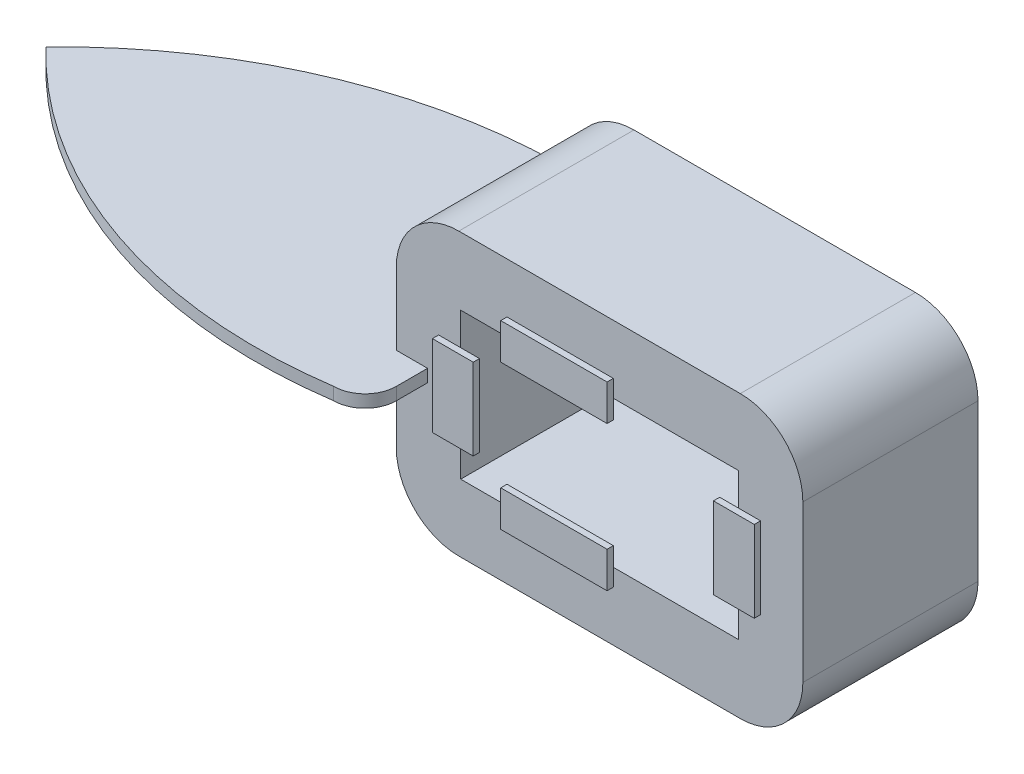
SolidWorks part; units mm, degrees
ref_plane "前基準面" through (0, 0, 0) normal (0, 0, 1) x (1, 0, 0)
ref_plane "上基準面" through (0, 0, 0) normal (0, 1, 0) x (1, 0, 0)
ref_plane "右基準面" through (0, 0, 0) normal (1, 0, 0) x (0, 0, -1)
sketch "草圖1" plane through (0, 0, 0) normal (0, 0, 1) x (1, 0, 0)
  line L0 (-9.02, 0) -> (7.9922, 0) construction
  line L2 (-59.9347, 22.5) -> (5.0653, 22.5)
  line L3 (-59.9347, 22.5) -> (-59.9347, -22.5)
  line L4 (-59.9347, -22.5) -> (5.0653, -22.5)
  line L5 (5.0653, 22.5) -> (5.0653, -22.5)
  dimension "D1" = 45
  dimension "D2" = 22.5
  dimension "D3" = 65
extrude "填料-伸長1" add sketch "草圖1" along normal blind 28
sketch "草圖2" plane through (0, 0, 0) normal (0, 0, 1) x (1, 0, 0)
  line L0 (-59.9347, 0) -> (5.361, 0) construction
  line L1 (-59.9347, 22.5) -> (-59.9347, -22.5) construction
  line L2 (-27.4347, 22.5) -> (-27.4347, -22.5) construction
  line L3 (5.0653, 22.5) -> (-59.9347, 22.5) construction
  line L4 (-59.9347, -22.5) -> (5.0653, -22.5) construction
  line L6 (-49.6347, 11.7) -> (-5.2347, 11.7)
  line L7 (-49.6347, 11.7) -> (-49.6347, -11.7)
  line L8 (-49.6347, -11.7) -> (-5.2347, -11.7)
  line L9 (-5.2347, 11.7) -> (-5.2347, -11.7)
  dimension "D1" = 44.4
  dimension "D2" = 23.4
  dimension "D3" = 10.3
  dimension "D4" = 10.8
extrude "除料-伸長1" cut sketch "草圖2" along normal blind 39
ref_plane "平面1" through (0, 0, 28) normal (0, 0, 1) x (1, 0, 0)
sketch "草圖3" plane through (0, 0, 28) normal (0, 0, 1) x (1, 0, 0)
  line L0 (-59.9347, 22.5) -> (-59.9347, -22.5) construction
  line L2 (-59.9347, 12) -> (-55.9347, 12)
  line L3 (-59.9347, 12) -> (-59.9347, -12)
  line L4 (-59.9347, -12) -> (-55.9347, -12)
  line L5 (-55.9347, 12) -> (-55.9347, -12)
  line L8 (-5.2347, -11.7) -> (-49.6347, -11.7) construction
  dimension "D1" = 4
  dimension "D2" = 24
  dimension "D3" = 0.3
ref_plane "平面2" through (-59.9347, 0, 0) normal (-1, 0, 0) x (0, 0, 1)
sketch "草圖6" plane through (0, 0, 28) normal (0, 0, 1) x (1, 0, 0)
  line L0 (-15.2347, 0.3) -> (5.0653, -22.5)
  line L1 (-5.2347, 11.7) -> (-5.2347, -11.7) construction
  line L2 (-5.2347, -11.7) -> (-49.6347, -11.7) construction
  line L3 (-15.2347, 0.3) -> (-15.2347, -22.5)
  line L4 (-59.9347, -22.5) -> (5.0653, -22.5) construction
  line L5 (-15.2347, -22.5) -> (5.0653, -22.5)
  dimension "D1" = 10
  dimension "D2" = 12
ref_plane "平面4" through (0, 0, 0) normal (0, 0, -1) x (-1, 0, 0)
fillet "圓角1" radius 10 1 edges at (-59.9347, -22.5, 14)
fillet "圓角2" radius 10 1 edges at (-59.9347, 22.5, 14)
fillet "圓角3" radius 10 1 edges at (5.0653, 22.5, 14)
fillet "圓角4" radius 10 1 edges at (5.0653, -22.5, 14)
ref_plane "平面6" through (0, 0, 29) normal (0, 0, 1) x (1, 0, 0)
sketch "草圖10" plane through (0, 0, 29) normal (0, 0, 1) x (1, 0, 0)
  line L6 (-49.6347, 0) -> (-4.2092, 0) construction
  line L7 (-49.6347, -11.7) -> (-49.6347, 11.7) construction
  line L8 (-27.4347, -11.7) -> (-27.4347, 19.297) construction
  line L9 (-5.2347, -11.7) -> (-49.6347, -11.7) construction
  line L11 (-49.6347, 6.5) -> (-53.1651, 6.5)
  line L14 (-53.1651, 6.5) -> (-53.1651, -6.5)
  line L17 (-49.6347, 6.5) -> (-46.6347, 6.5)
  line L18 (-46.6347, 6.5) -> (-46.6347, -6.5)
  line L20 (-42.2347, -11.7) -> (-42.2347, -8.7)
  line L25 (-42.2347, -11.7) -> (-42.2347, -14.4546)
  line L27 (-8.2347, 6.5) -> (-8.2347, -6.5)
  line L28 (-8.2347, -6.5) -> (-5.2347, -6.5)
  line L29 (-5.2347, -6.5) -> (-1.7043, -6.5)
  line L30 (-1.7043, 6.5) -> (-1.7043, -6.5)
  line L32 (-25.2347, 8.7) -> (-25.2347, 14.4546)
  line L33 (-25.2347, -14.4546) -> (-25.2347, -8.7)
  line L34 (-25.2347, -14.4546) -> (-42.2347, -14.4546)
  line L35 (-25.2347, -8.7) -> (-42.2347, -8.7)
  line L36 (-25.2347, 8.7) -> (-42.2347, 8.7)
  line L37 (-25.2347, 14.4546) -> (-42.2347, 14.4546)
  line L38 (-42.2347, 8.7) -> (-42.2347, 14.4546)
  line L39 (-46.6347, -6.5) -> (-53.1651, -6.5)
  line L40 (-1.7043, 6.5) -> (-8.2347, 6.5)
  dimension "D3" = 13
  dimension "D4" = 6.5
extrude "填料-伸長6" add sketch "草圖10" against normal blind 1 separate body
sketch "草圖19" plane through (0, 0, 0) normal (0, 1, 0) x (1, 0, 0)
  line L0 (-59.9347, 6.325) -> (-59.9347, -6.325) construction
  line L1 (-59.9347, 1.0971) -> (-54.9347, 1.0971)
  line L2 (-59.9347, 1.0971) -> (-59.9347, -29)
  line L3 (-59.9347, -29) -> (-54.9347, -29)
  line L4 (-54.9347, 1.0971) -> (-54.9347, -29)
  line L5 (-24.75, -29) -> (24.75, -29) construction
  dimension "D1" = 5
ref_plane "平面7" through (0, 0, 28) normal (0, 0, 1) x (1, 0, 0)
sketch "草圖20" plane through (0, 0, 28) normal (0, 0, 1) x (1, 0, 0)
  line L0 (-59.9347, 12.5) -> (-59.9347, -12.5) construction
  line L1 (-59.9347, 1) -> (-54.932, 1)
  line L2 (-59.9347, 1) -> (-59.9347, -1)
  line L3 (-59.9347, -1) -> (-54.932, -1)
  line L4 (-54.932, 1) -> (-54.932, -1)
  line L5 (-59.9347, 0) -> (-54.9347, 0) construction
  dimension "D1" = 5.0026
  dimension "D2" = 2
  dimension "D3" = 1
extrude "填料-伸長7" add sketch "草圖20" along normal blind 10
ref_plane "平面8" through (0, 0, 0) normal (0, 0, -1) x (-1, 0, 0)
sketch "草圖21" plane through (0, 0, 0) normal (0, 0, -1) x (-1, 0, 0)
  line L0 (59.9347, 0) -> (54.9347, 0) construction
  line L1 (54.9323, 1) -> (59.9347, 1)
  line L2 (54.9323, 1) -> (54.9323, -1)
  line L3 (54.9323, -1) -> (59.9347, -1)
  line L4 (59.9347, 1) -> (59.9347, -1)
  dimension "D1" = 5.0023
  dimension "D2" = 2
  dimension "D3" = 1
extrude "填料-伸長8" add sketch "草圖21" along normal blind 10
sketch "草圖22" plane through (0, 0, 0) normal (0, 1, 0) x (1, 0, 0)
  line L1 (-59.9347, 10) -> (-59.9347, -38)
  line L2 (-59.9347, -14) -> (-129.9347, -14) construction
  arc A2 (-129.9347, -14) -> (-59.9347, 10) centre (-71.5653, -70.1606) cw
  arc A3 (-129.9347, -14) -> (-59.9347, -38) centre (-71.5653, 42.1606) ccw
  dimension "D2" = 81
  dimension "D3" = 81
  dimension "D4" = 48
  dimension "D1" = 70
extrude "填料-伸長9" add sketch "草圖22" along normal blind 1 and the other way blind 1
fillet "圓角5" radius 5 1 edges at (-54.9323, 0, -10)
fillet "圓角6" radius 5 1 edges at (-54.932, 0, 38)
